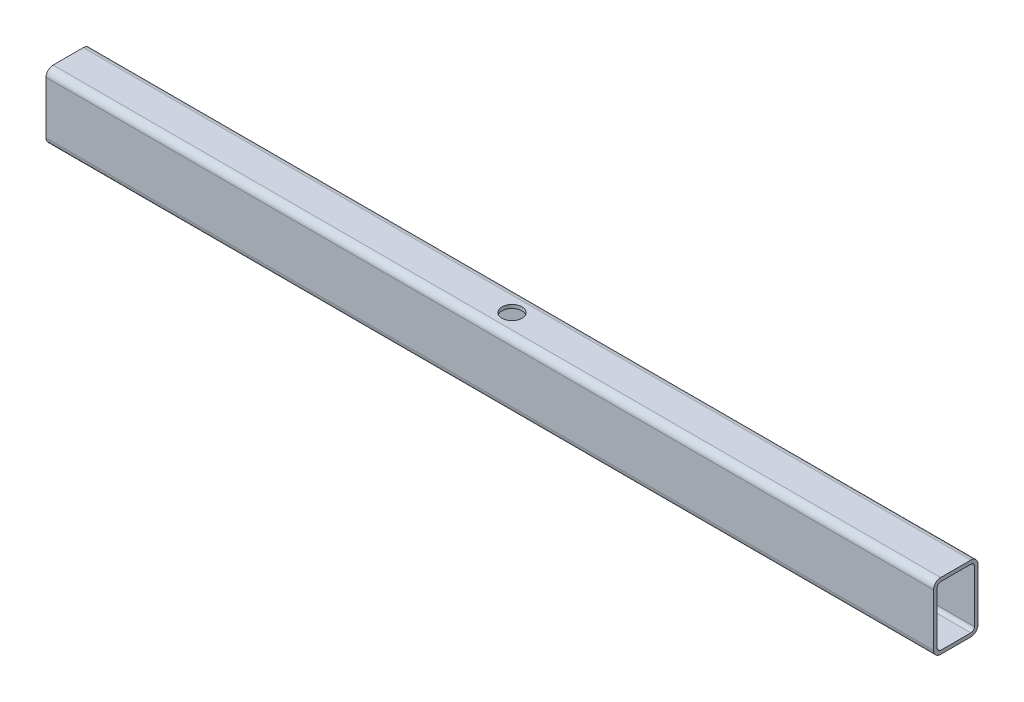
SolidWorks part; units mm, degrees
ref_plane "Ön Düzlem" through (0, 0, 0) normal (0, 0, 1) x (1, 0, 0)
ref_plane "Üst Düzlem" through (0, 0, 0) normal (0, 1, 0) x (1, 0, 0)
ref_plane "Sağ Düzlem" through (0, 0, 0) normal (1, 0, 0) x (0, 0, -1)
sketch3d "3B Çizim1"
  line L0 (0, 0, 0) -> (800, 0, 0)
  dimension "D1" = 800
other "Dikdörtgen tüp 60 X 40 X 3.2(1)"
ref_plane "Düzlem1" through (0, 0, 0) normal (1, 0, 0) x (0, 0, -1)
sketch "Sketch1" plane through (0, 0, 0) normal (1, 0, 0) x (0, 0, -1)
  line L0 (-13.6, -26.8) -> (13.6, -26.8)
  line L1 (-16.8, -23.6) -> (-16.8, 23.6)
  line L2 (13.6, 26.8) -> (-13.6, 26.8)
  line L3 (16.8, 23.6) -> (16.8, -23.6)
  line L4 (-13.6, -30) -> (13.6, -30)
  line L5 (-20, -23.6) -> (-20, 23.6)
  line L6 (13.6, 30) -> (-13.6, 30)
  line L7 (20, 23.6) -> (20, -23.6)
  arc A0 (20, 23.6) -> (13.6, 30) centre (13.6, 23.6) ccw
  arc A1 (13.6, -30) -> (20, -23.6) centre (13.6, -23.6) ccw
  arc A2 (-20, -23.6) -> (-13.6, -30) centre (-13.6, -23.6) ccw
  arc A3 (-13.6, 30) -> (-20, 23.6) centre (-13.6, 23.6) ccw
  arc A4 (-13.6, 26.8) -> (-16.8, 23.6) centre (-13.6, 23.6) ccw
  arc A5 (16.8, 23.6) -> (13.6, 26.8) centre (13.6, 23.6) ccw
  arc A6 (13.6, -26.8) -> (16.8, -23.6) centre (13.6, -23.6) ccw
  arc A7 (-16.8, -23.6) -> (-13.6, -26.8) centre (-13.6, -23.6) ccw
  point P0 (0, 30)
  point P1 (20, 0)
  point P2 (0, -30)
  point P3 (-20, 0)
  point P4 (-20, 30)
  point P5 (20, 30)
  point P6 (20, -30)
  point P7 (-20, -30)
  point P8 (0, 0)
  point P33 (0, 0)
  dimension "D1" = 6.4
  dimension "Thickness" = 3.2
  dimension "V_leg" = 60
  dimension "H_leg" = 40
sketch "Çizim3" plane through (0, 0, 0) normal (0, 1, 0) x (1, 0, 0)
  line L0 (0, 0) -> (800, 0) construction
  circle A0 centre (400, 0) radius 9
  dimension "D1" = 18
extrude "Kes-Ekstrüzyon1" cut sketch "Çizim3" against normal mid plane 100
scale "Scale1" scale about origin uniform scaling yes scale factor 0.25
